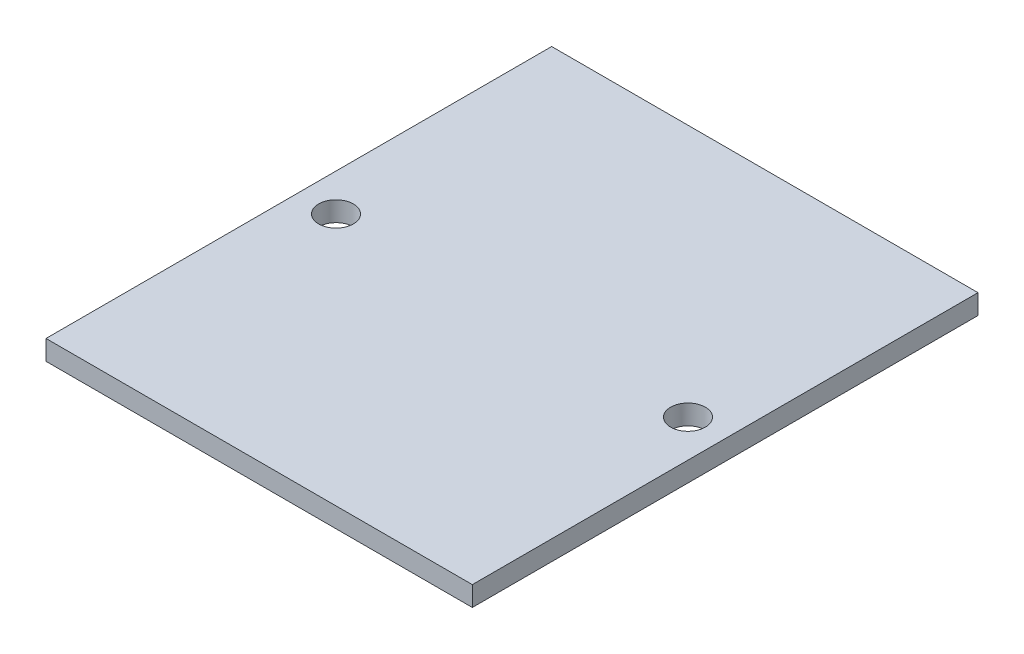
SolidWorks part; units mm, degrees
ref_plane "Front Plane" through (0, 0, 0) normal (0, 0, 1) x (1, 0, 0)
ref_plane "Top Plane" through (0, 0, 0) normal (0, 1, 0) x (1, 0, 0)
ref_plane "Right Plane" through (0, 0, 0) normal (1, 0, 0) x (0, 0, -1)
sketch "Sketch1" plane through (0, 0, 0) normal (0, 1, 0) x (1, 0, 0)
  line L1 (21.5, -25.5) -> (-21.5, -25.5)
  line L2 (21.5, -25.5) -> (21.5, 25.5)
  line L3 (21.5, 25.5) -> (-21.5, 25.5)
  line L4 (-21.5, -25.5) -> (-21.5, 25.5)
  line L5 (21.5, -25.5) -> (-21.5, 25.5) construction
  line L6 (21.5, 25.5) -> (-21.5, -25.5) construction
  point P0 (0, 0)
  dimension "D1" = 43
  dimension "D2" = 51
extrude "Boss-Extrude1" add sketch "Sketch1" along normal blind 2
sketch "Sketch2" plane through (0, 2, 0) normal (0, 1, 0) x (1, 0, 0)
  line L0 (21.5, 0) -> (-21.5, 0) construction
  line L1 (-21.5, 25.5) -> (-21.5, -25.5) construction
  line L2 (0, -25.5) -> (0, 25.5) construction
  line L3 (21.5, 25.5) -> (-21.5, 25.5) construction
  circle A0 centre (-17.75, 0) radius 1.75
  circle A1 centre (17.75, 0) radius 1.75
  point P6 (0, 0)
  point P12 (0, 0)
  dimension "D1" = 3.5
  dimension "D2" = 3.75
extrude "Cut-Extrude1" cut sketch "Sketch2" against normal up to surface (2 mm away) up to face at (0, 0, 0)
